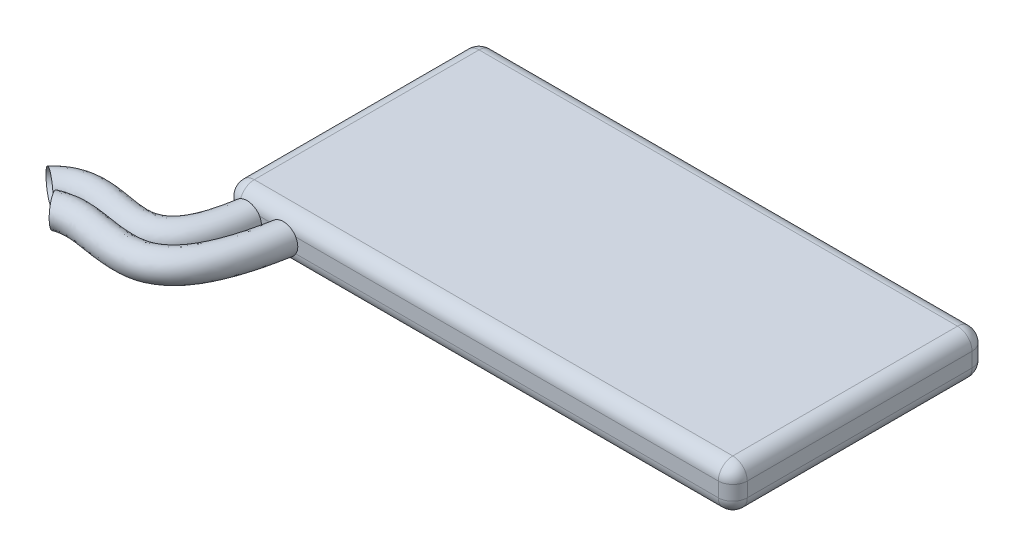
SolidWorks part; units mm, degrees
ref_plane "Front Plane" through (0, 0, 0) normal (0, 0, 1) x (1, 0, 0)
ref_plane "Top Plane" through (0, 0, 0) normal (0, 1, 0) x (1, 0, 0)
ref_plane "Right Plane" through (0, 0, 0) normal (1, 0, 0) x (0, 0, -1)
sketch "Sketch1" plane through (0, 0, 0) normal (0, 1, 0) x (1, 0, 0)
  line L1 (0, 0) -> (70, 0)
  line L2 (0, 0) -> (0, 35)
  line L3 (0, 35) -> (70, 35)
  line L4 (70, 0) -> (70, 35)
  point P0 (0, 0)
  dimension "D1" = 70
  dimension "D2" = 35
extrude "Boss-Extrude1" add sketch "Sketch1" along normal blind 6
sketch "Sketch2" plane through (0, 0, 0) normal (0, 0, 1) x (1, 0, 0)
  line L0 (0, 3) -> (3, 3) construction
  line L1 (0, 6) -> (0, 0) construction
  circle A0 centre (3, 3) radius 2
  dimension "D1" = 4
  dimension "D2" = 3
sketch3d "3DSketch1"
  spline S0 degree 3 poles (3, 3, 0) (0.4518, 2.9122, 16.0453) (-8.5459, 2.9545, 3.7594) (-14.4226, 2.9225, 9.8207) knots 0 0 0 0 1 1 1 1
  dimension "D1" = 13
  dimension "D2" = 15
  dimension "D3" = 20
surface "Surface-Sweep1"
sketch "Sketch3" plane through (0, 0, 0) normal (0, 0, 1) x (1, 0, 0)
  line L0 (0, 3) -> (8, 3) construction
  line L1 (0, 6) -> (0, 0) construction
  circle A0 centre (8, 3) radius 2
  dimension "D1" = 8
  dimension "D2" = 4
sketch3d "3DSketch2"
  spline S0 degree 3 poles (8, 3, 0) (6.0627, 3.2544, 12.5461) (-4.2365, 2.7264, 13.2358) (-8.3949, 2.7875, 11.0982) (-11.2284, 2.9391, 12.3903) knots 0 0 0 0 0.456377 1 1 1 1
surface "Surface-Sweep2"
fillet "Fillet1" radius 2 12 edges at (35, 0, -35) (0, 0, -17.5) (0, 3, -35) (0, 3, 0) (0, 6, -17.5) (35, 0, 0) (70, 0, -17.5) (70, 3, -35) (70, 3, 0) (70, 6, -17.5) (35, 6, -35) (35, 6, 0)
